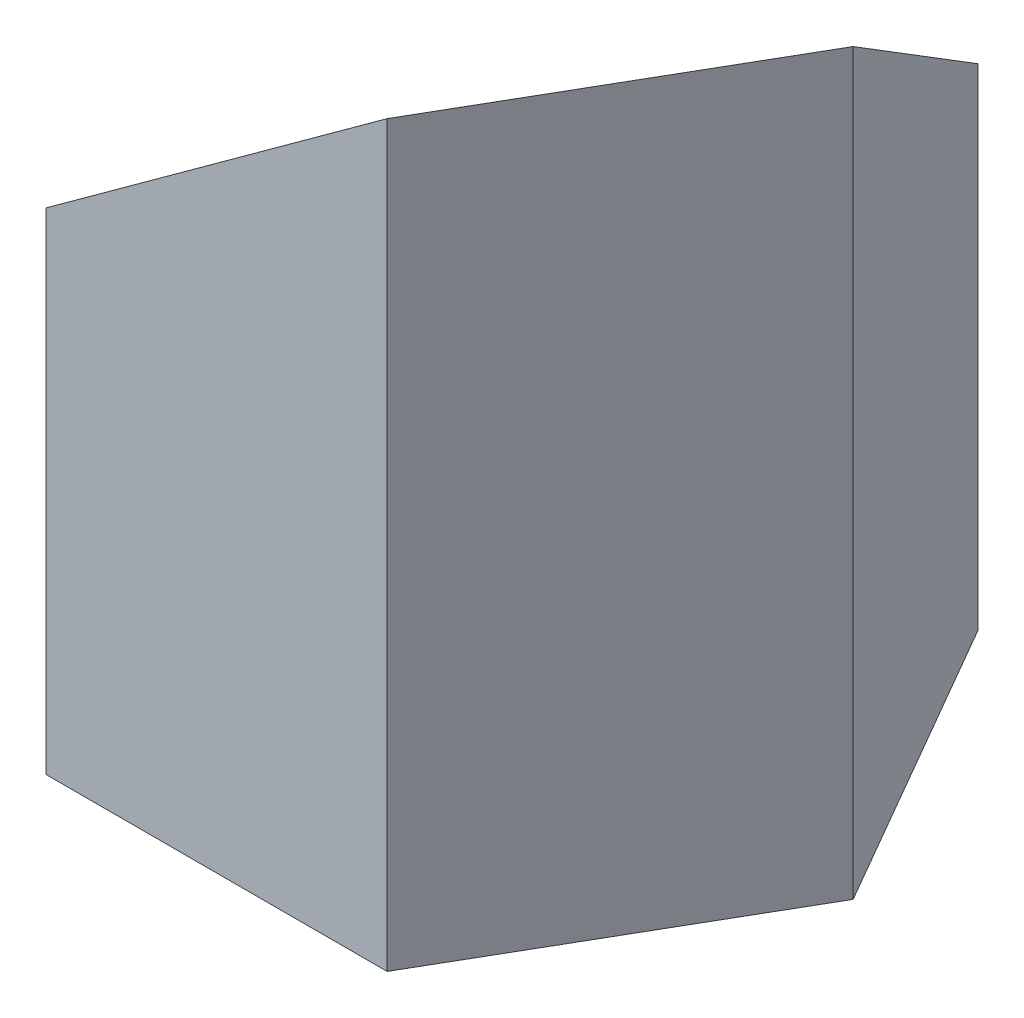
SolidWorks part; units mm, degrees
ref_plane "Front Plane" through (0, 0, 0) normal (0, 0, 1) x (1, 0, 0)
ref_plane "Top Plane" through (0, 0, 0) normal (0, 1, 0) x (1, 0, 0)
ref_plane "Right Plane" through (0, 0, 0) normal (1, 0, 0) x (0, 0, -1)
sketch "Sketch1" plane through (0, 0, 0) normal (0, 1, 0) x (1, 0, 0)
  line L1 (46.188, 0) -> (23.094, 40)
  line L2 (23.094, 40) -> (-23.094, 40)
  line L3 (-23.094, 40) -> (-46.188, 0)
  line L4 (-46.188, 0) -> (-23.094, -40)
  line L5 (-23.094, -40) -> (23.094, -40)
  line L6 (23.094, -40) -> (46.188, 0)
  circle A0 centre (0, 0) radius 40 construction
  circle A1 centre (0, 0) radius 12.5
  dimension "D1" = 25
  dimension "D2" = 80
extrude "Boss-Extrude1" add sketch "Sketch1" along normal blind 100
draft "Draft8" type of draft neutral plane draft angle 40 faces to draft 1 face at (0, 100, 0) neutral plane through (23.094, 100, 40) neutral plane normal (0.866, 0, 0.5) reverse direction yes parameters "D1"=40
